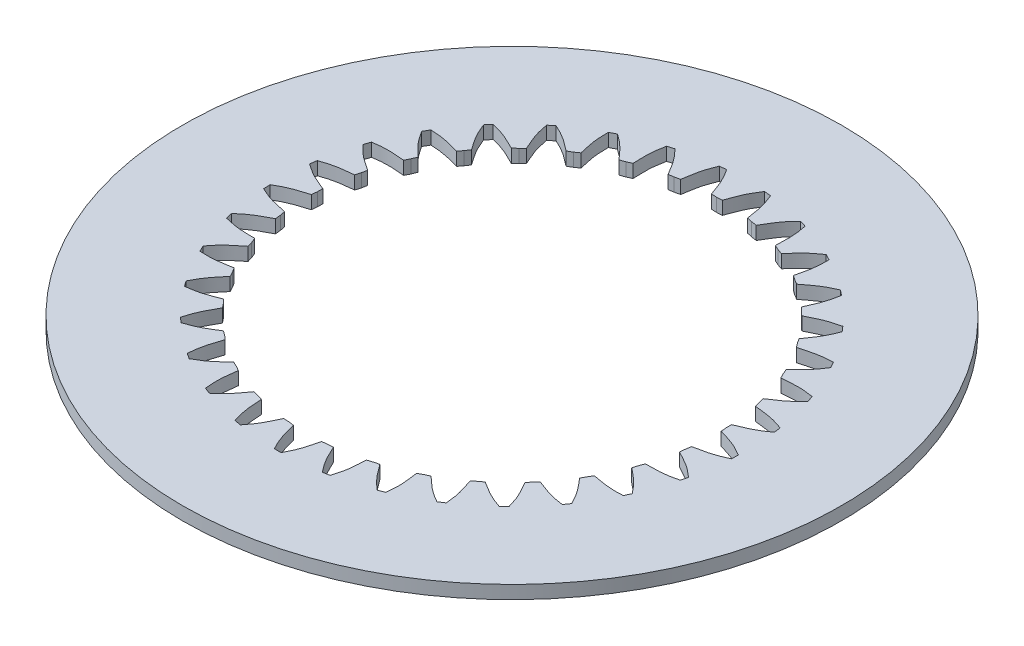
SolidWorks part; units mm, degrees
ref_plane "Plano frontal" through (0, 0, 0) normal (0, 0, 1) x (1, 0, 0)
ref_plane "Plano superior" through (0, 0, 0) normal (0, 1, 0) x (1, 0, 0)
ref_plane "Plano direito" through (0, 0, 0) normal (1, 0, 0) x (0, 0, -1)
sketch "Esboço1" plane through (0, 0, 0) normal (0, 1, 0) x (1, 0, 0)
  line L100 (-38.3877, -48.814) -> (-37.1388, -49.8771)
  line L101 (-39.3009, -59.2517) -> (-37.5711, -60.3634)
  line L102 (-29.9418, -54.5024) -> (-28.4559, -55.1967)
  line L103 (-28.4559, -55.1967) -> (-27.0284, -56.0043)
  line L104 (-27.3773, -65.6187) -> (-25.4682, -66.383)
  line L105 (-19.0861, -59.184) -> (-17.4956, -59.5846)
  line L106 (-17.4956, -59.5846) -> (-15.941, -60.1074)
  line L107 (-14.4641, -69.6141) -> (-12.4449, -70.0032)
  line L108 (-7.5405, -61.7265) -> (-5.903, -61.8189)
  line L109 (-5.903, -61.8189) -> (-4.2776, -62.0381)
  line L110 (-1.0282, -71.0934) -> (1.0282, -71.0934)
  line L111 (4.2776, -62.0381) -> (5.903, -61.8189)
  line L112 (5.903, -61.8189) -> (7.5405, -61.7265)
  line L113 (12.4449, -70.0032) -> (14.4641, -69.6141)
  line L114 (15.941, -60.1074) -> (17.4956, -59.5846)
  line L115 (17.4956, -59.5846) -> (19.0861, -59.184)
  line L116 (25.4682, -66.383) -> (27.3772, -65.6187)
  line L117 (27.0284, -56.0043) -> (28.4559, -55.1967)
  line L118 (28.4559, -55.1967) -> (29.9418, -54.5024)
  line L119 (37.5711, -60.3634) -> (39.3009, -59.2517)
  line L120 (37.1388, -49.8771) -> (38.3877, -48.814)
  line L121 (38.3877, -48.814) -> (39.7154, -47.8509)
  line L122 (48.3159, -52.1622) -> (49.8042, -50.7432)
  line L123 (45.907, -41.9472) -> (46.9321, -40.6669)
  line L124 (46.9321, -40.6669) -> (48.0535, -39.47)
  line L125 (57.3146, -42.0757) -> (58.5074, -40.4007)
  line L126 (53.016, -32.5012) -> (53.7802, -31.05)
  line L127 (53.7802, -31.05) -> (54.6549, -29.6626)
  line L128 (64.2417, -30.4685) -> (65.0959, -28.598)
  line L129 (58.2088, -21.8805) -> (58.6846, -20.3109)
  line L130 (58.6846, -20.3109) -> (59.2808, -18.783)
  line L131 (68.847, -17.7601) -> (69.3318, -15.7617)
  line L132 (61.2978, -10.469) -> (61.468, -8.8378)
  line L133 (61.468, -8.8378) -> (61.7643, -7.2246)
  line L134 (70.9639, -4.4098) -> (71.0618, -2.3558)
  line L135 (62.1713, 1.3208) -> (62.0297, 2.9548)
  line L136 (62.0297, 2.9548) -> (62.0154, 4.5949)
  line L137 (70.5161, 9.1) -> (70.2234, 11.1353)
  line L138 (60.7979, 13.063) -> (60.3496, 14.6406)
  line L139 (60.3496, 14.6406) -> (60.0251, 16.2484)
  line L140 (67.5196, 22.2808) -> (66.847, 24.224)
  line L141 (57.227, 24.333) -> (56.4882, 25.7973)
  line L142 (56.4882, 25.7973) -> (55.8653, 27.3146)
  line L143 (62.0828, 34.6563) -> (61.0546, 36.4371)
  line L144 (51.5878, 34.7235) -> (50.5852, 36.0216)
  line L145 (50.5852, 36.0216) -> (49.6865, 37.3935)
  line L146 (54.4021, 45.7792) -> (53.0555, 47.3333)
  line L147 (44.084, 43.8591) -> (42.854, 44.9439)
  line L148 (42.854, 44.9439) -> (41.7118, 46.121)
  line L149 (44.7552, 55.2476) -> (43.1388, 56.5187)
  line L150 (34.987, 51.4094) -> (33.5738, 52.2419)
  line L151 (33.5738, 52.2419) -> (32.2295, 53.1815)
  line L152 (33.4907, 62.7192) -> (31.663, 63.6615)
  line L153 (24.6254, 57.1017) -> (23.0803, 57.6517)
  line L154 (23.0803, 57.6517) -> (21.5824, 58.32)
  line L155 (21.0158, 67.9239) -> (19.0428, 68.5033)
  line L156 (13.3739, 60.7302) -> (11.7525, 60.9778)
  line L157 (11.7525, 60.9778) -> (10.1553, 61.3506)
  line L158 (7.7814, 70.6737) -> (5.7344, 70.8692)
  line L159 (1.6389, 62.1638) -> (0, 62.1001)
  line L160 (0, 62.1001) -> (-1.6389, 62.1638)
  line L161 (-5.7344, 70.8692) -> (-7.7814, 70.6737)
  line L162 (-10.1553, 61.3506) -> (-11.7525, 60.9778)
  line L163 (-11.7525, 60.9778) -> (-13.3739, 60.7302)
  line L164 (-19.0428, 68.5033) -> (-21.0158, 67.924)
  line L165 (-21.5824, 58.32) -> (-23.0803, 57.6517)
  line L166 (-23.0803, 57.6517) -> (-24.6254, 57.1017)
  line L167 (-31.663, 63.6615) -> (-33.4907, 62.7192)
  line L168 (-32.2295, 53.1815) -> (-33.5738, 52.2419)
  line L169 (-33.5738, 52.2419) -> (-34.987, 51.4094)
  line L170 (-43.1388, 56.5187) -> (-44.7552, 55.2476)
  line L171 (-41.7118, 46.121) -> (-42.854, 44.9439)
  line L172 (-42.854, 44.9439) -> (-44.084, 43.8591)
  line L173 (-53.0555, 47.3333) -> (-54.4021, 45.7792)
  line L174 (-49.6865, 37.3935) -> (-50.5852, 36.0216)
  line L175 (-50.5852, 36.0216) -> (-51.5878, 34.7235)
  line L176 (-61.0546, 36.4371) -> (-62.0828, 34.6563)
  line L177 (-55.8653, 27.3146) -> (-56.4882, 25.7973)
  line L178 (-56.4882, 25.7973) -> (-57.227, 24.333)
  line L179 (-66.847, 24.224) -> (-67.5196, 22.2808)
  line L180 (-60.0251, 16.2484) -> (-60.3496, 14.6407)
  line L181 (-60.3496, 14.6407) -> (-60.7979, 13.063)
  line L182 (-70.2234, 11.1353) -> (-70.5161, 9.1)
  line L183 (-62.0154, 4.5949) -> (-62.0297, 2.9548)
  line L184 (-62.0297, 2.9548) -> (-62.1713, 1.3208)
  line L185 (-71.0618, -2.3558) -> (-70.9639, -4.4097)
  line L186 (-61.7643, -7.2246) -> (-61.468, -8.8378)
  line L187 (-61.468, -8.8378) -> (-61.2978, -10.469)
  line L188 (-69.3318, -15.7617) -> (-68.847, -17.7601)
  line L189 (-59.2808, -18.783) -> (-58.6846, -20.3109)
  line L190 (-58.6846, -20.3109) -> (-58.2088, -21.8805)
  line L191 (-65.0959, -28.598) -> (-64.2417, -30.4685)
  line L192 (-54.6549, -29.6626) -> (-53.7802, -31.05)
  line L193 (-53.7802, -31.05) -> (-53.016, -32.5012)
  line L194 (-58.5074, -40.4007) -> (-57.3146, -42.0757)
  line L195 (-48.0535, -39.47) -> (-46.9321, -40.6669)
  line L196 (-46.9321, -40.6669) -> (-45.907, -41.9472)
  line L197 (-49.8042, -50.7432) -> (-48.316, -52.1622)
  line L198 (-39.7154, -47.8509) -> (-38.3877, -48.814)
  circle A1 centre (0, 0) radius 100
  spline S132 degree 3 poles (-37.1388, -49.8771) (-37.3893, -50.6396) (-37.8968, -52.1594) (-38.8582, -55.2403) (-39.1757, -57.6479) (-39.3009, -59.2517) knots -0.006202 -0.006202 -0.006202 -0.006202 0.243606 0.493415 0.993031 0.993031 0.993031 0.993031
  spline S133 degree 3 poles (-37.5711, -60.3634) (-36.1642, -59.5833) (-34.1061, -58.2943) (-31.703, -56.14) (-30.5314, -55.0469) (-29.9418, -54.5024) knots -0.006202 -0.006202 -0.006202 -0.006202 0.493415 0.743223 0.993031 0.993031 0.993031 0.993031
  spline S134 degree 3 poles (-27.0284, -56.0043) (-27.13, -56.8005) (-27.3407, -58.3889) (-27.7017, -61.596) (-27.5578, -64.0202) (-27.3773, -65.6187) knots -0.006202 -0.006202 -0.006202 -0.006202 0.243606 0.493415 0.993031 0.993031 0.993031 0.993031
  spline S135 degree 3 poles (-25.4682, -66.383) (-24.2345, -65.3507) (-22.4575, -63.6955) (-20.5055, -61.1253) (-19.5619, -59.8302) (-19.0861, -59.184) knots -0.006202 -0.006202 -0.006202 -0.006202 0.493415 0.743223 0.993031 0.993031 0.993031 0.993031
  spline S136 degree 3 poles (-15.941, -60.1074) (-15.8901, -60.9084) (-15.7965, -62.508) (-15.544, -65.7255) (-14.9439, -68.0786) (-14.4641, -69.6141) knots -0.006202 -0.006202 -0.006202 -0.006202 0.243606 0.493415 0.993031 0.993031 0.993031 0.993031
  spline S137 degree 3 poles (-12.4449, -70.0032) (-11.4288, -68.7561) (-9.9972, -66.7946) (-8.5669, -63.9014) (-7.8855, -62.4512) (-7.5405, -61.7265) knots -0.006202 -0.006202 -0.006202 -0.006202 0.493415 0.743223 0.993031 0.993031 0.993031 0.993031
  spline S138 degree 3 poles (-4.2776, -62.0381) (-4.076, -62.8149) (-3.6813, -64.3679) (-2.8244, -67.4795) (-1.7899, -69.6765) (-1.0282, -71.0934) knots -0.006202 -0.006202 -0.006202 -0.006202 0.243606 0.493415 0.993031 0.993031 0.993031 0.993031
  spline S139 degree 3 poles (1.0282, -71.0934) (1.7899, -69.6765) (2.8244, -67.4795) (3.6813, -64.3679) (4.076, -62.8149) (4.2776, -62.0381) knots -0.006202 -0.006202 -0.006202 -0.006202 0.493415 0.743223 0.993031 0.993031 0.993031 0.993031
  spline S140 degree 3 poles (7.5405, -61.7265) (7.8855, -62.4512) (8.5669, -63.9014) (9.9972, -66.7946) (11.4288, -68.7561) (12.4449, -70.0032) knots -0.006202 -0.006202 -0.006202 -0.006202 0.243606 0.493415 0.993031 0.993031 0.993031 0.993031
  spline S141 degree 3 poles (14.4641, -69.6141) (14.9439, -68.0786) (15.544, -65.7255) (15.7965, -62.508) (15.8901, -60.9084) (15.941, -60.1074) knots -0.006202 -0.006202 -0.006202 -0.006202 0.493415 0.743223 0.993031 0.993031 0.993031 0.993031
  spline S142 degree 3 poles (19.0861, -59.184) (19.5619, -59.8302) (20.5055, -61.1253) (22.4575, -63.6955) (24.2345, -65.3507) (25.4682, -66.383) knots -0.006202 -0.006202 -0.006202 -0.006202 0.243606 0.493415 0.993031 0.993031 0.993031 0.993031
  spline S143 degree 3 poles (27.3772, -65.6187) (27.5578, -64.0202) (27.7017, -61.5961) (27.3407, -58.3889) (27.13, -56.8005) (27.0284, -56.0043) knots -0.006202 -0.006202 -0.006202 -0.006202 0.493415 0.743223 0.993031 0.993031 0.993031 0.993031
  spline S144 degree 3 poles (29.9418, -54.5024) (30.5314, -55.0469) (31.703, -56.14) (34.1061, -58.2944) (36.1642, -59.5833) (37.5711, -60.3634) knots -0.006202 -0.006202 -0.006202 -0.006202 0.243606 0.493415 0.993031 0.993031 0.993031 0.993031
  spline S145 degree 3 poles (39.3009, -59.2517) (39.1757, -57.6479) (38.8582, -55.2404) (37.8968, -52.1594) (37.3893, -50.6396) (37.1388, -49.8771) knots -0.006202 -0.006202 -0.006202 -0.006202 0.493415 0.743223 0.993031 0.993031 0.993031 0.993031
  spline S146 degree 3 poles (39.7154, -47.8509) (40.3973, -48.2741) (41.7546, -49.1256) (44.522, -50.7863) (46.7869, -51.6624) (48.3159, -52.1622) knots -0.006202 -0.006202 -0.006202 -0.006202 0.243606 0.493415 0.993031 0.993031 0.993031 0.993031
  spline S147 degree 3 poles (49.8042, -50.7432) (49.3777, -49.1921) (48.6103, -46.8881) (47.0832, -44.0448) (46.2972, -42.6485) (45.907, -41.9472) knots -0.006202 -0.006202 -0.006202 -0.006202 0.493415 0.743223 0.993031 0.993031 0.993031 0.993031
  spline S148 degree 3 poles (48.0535, -39.47) (48.8032, -39.7564) (50.2972, -40.3358) (53.3288, -41.4426) (55.7186, -41.8743) (57.3146, -42.0757) knots -0.006202 -0.006202 -0.006202 -0.006202 0.243606 0.493415 0.993031 0.993031 0.993031 0.993031
  spline S149 degree 3 poles (58.5074, -40.4007) (57.795, -38.9583) (56.6055, -36.8412) (54.5679, -34.3383) (53.5318, -33.116) (53.016, -32.5012) knots -0.006202 -0.006202 -0.006202 -0.006202 0.493415 0.743223 0.993031 0.993031 0.993031 0.993031
  spline S150 degree 3 poles (54.6549, -29.6626) (55.4452, -29.8019) (57.0218, -30.088) (60.2082, -30.6012) (62.6364, -30.5728) (64.2417, -30.4685) knots -0.006202 -0.006202 -0.006202 -0.006202 0.243606 0.493415 0.993031 0.993031 0.993031 0.993031
  spline S151 degree 3 poles (65.0959, -28.598) (64.1235, -27.3165) (62.5548, -25.4628) (60.0804, -23.3907) (58.8317, -22.3866) (58.2088, -21.8805) knots -0.006202 -0.006202 -0.006202 -0.006202 0.493415 0.743223 0.993031 0.993031 0.993031 0.993031
  spline S152 degree 3 poles (59.2808, -18.783) (60.0833, -18.7703) (61.6856, -18.7529) (64.9115, -18.6537) (67.2904, -18.1663) (68.847, -17.7601) knots -0.006202 -0.006202 -0.006202 -0.006202 0.243606 0.493415 0.993031 0.993031 0.993031 0.993031
  spline S153 degree 3 poles (69.3318, -15.7617) (68.1344, -14.6874) (66.2432, -13.1641) (63.4214, -11.5978) (62.0052, -10.8481) (61.2978, -10.469) knots -0.006202 -0.006202 -0.006202 -0.006202 0.493415 0.743223 0.993031 0.993031 0.993031 0.993031
  spline S154 degree 3 poles (61.7643, -7.2246) (62.5498, -7.0602) (64.1198, -6.7399) (67.2687, -6.032) (69.5124, -5.1032) (70.9639, -4.4098) knots -0.006202 -0.006202 -0.006202 -0.006202 0.243606 0.493415 0.993031 0.993031 0.993031 0.993031
  spline S155 degree 3 poles (71.0618, -2.3558) (69.6827, -1.5275) (67.5374, -0.3896) (64.4701, 0.6144) (62.9377, 1.0825) (62.1713, 1.3208) knots -0.006202 -0.006202 -0.006202 -0.006202 0.493415 0.743223 0.993031 0.993031 0.993031 0.993031
  spline S156 degree 3 poles (62.0154, 4.5949) (62.7556, 4.905) (64.2366, 5.5167) (67.1946, 6.8076) (69.222, 8.1443) (70.5161, 9.1) knots -0.006202 -0.006202 -0.006202 -0.006202 0.243606 0.493415 0.993031 0.993031 0.993031 0.993031
  spline S157 degree 3 poles (70.2234, 11.1353) (68.7126, 11.6877) (66.3907, 12.399) (63.1888, 12.8043) (61.5955, 12.974) (60.7979, 13.063) knots -0.006202 -0.006202 -0.006202 -0.006202 0.493415 0.743223 0.993031 0.993031 0.993031 0.993031
  spline S158 degree 3 poles (60.0251, 16.2484) (60.6933, 16.6929) (62.0318, 17.5738) (64.6919, 19.4013) (66.4298, 21.0975) (67.5196, 22.2808) knots -0.006202 -0.006202 -0.006202 -0.006202 0.243606 0.493415 0.993031 0.993031 0.993031 0.993031
  spline S159 degree 3 poles (66.847, 24.224) (65.2589, 24.4804) (62.8444, 24.7395) (59.6237, 24.5315) (58.027, 24.3966) (57.227, 24.333) knots -0.006202 -0.006202 -0.006202 -0.006202 0.493415 0.743223 0.993031 0.993031 0.993031 0.993031
  spline S160 degree 3 poles (55.8653, 27.3146) (56.4373, 27.8775) (57.5849, 28.9958) (59.8512, 31.2937) (61.2366, 33.2882) (62.0828, 34.6563) knots -0.006202 -0.006202 -0.006202 -0.006202 0.243606 0.493415 0.993031 0.993031 0.993031 0.993031
  spline S161 degree 3 poles (61.0546, 36.4371) (59.4467, 36.3883) (57.0267, 36.1858) (53.9036, 35.3721) (52.3613, 34.9374) (51.5878, 34.7235) knots -0.006202 -0.006202 -0.006202 -0.006202 0.493415 0.743223 0.993031 0.993031 0.993031 0.993031
  spline S162 degree 3 poles (49.6865, 37.3935) (50.1416, 38.0546) (51.0568, 39.3699) (52.8472, 42.0551) (53.8301, 44.2757) (54.4021, 45.7792) knots -0.006202 -0.006202 -0.006202 -0.006202 0.243606 0.493415 0.993031 0.993031 0.993031 0.993031
  spline S163 degree 3 poles (53.0555, 47.3333) (51.4859, 46.9811) (49.148, 46.3242) (46.2353, 44.9342) (44.8031, 44.2155) (44.084, 43.8591) knots -0.006202 -0.006202 -0.006202 -0.006202 0.493415 0.743223 0.993031 0.993031 0.993031 0.993031
  spline S164 degree 3 poles (41.7118, 46.121) (42.0336, 46.8562) (42.6833, 48.3209) (43.9332, 51.2965) (44.4781, 53.663) (44.7552, 55.2476) knots -0.006202 -0.006202 -0.006202 -0.006202 0.243606 0.493415 0.993031 0.993031 0.993031 0.993031
  spline S165 degree 3 poles (43.1388, 56.5187) (41.6642, 55.8759) (39.4929, 54.7884) (36.8959, 52.8722) (35.6257, 51.8955) (34.987, 51.4094) knots -0.006202 -0.006202 -0.006202 -0.006202 0.493415 0.743223 0.993031 0.993031 0.993031 0.993031
  spline S166 degree 3 poles (32.2295, 53.1815) (32.4064, 53.9644) (32.7672, 55.5256) (33.4313, 58.6839) (33.5185, 61.1108) (33.4907, 62.7192) knots -0.006202 -0.006202 -0.006202 -0.006202 0.243606 0.493415 0.993031 0.993031 0.993031 0.993031
  spline S167 degree 3 poles (31.663, 63.6615) (30.3367, 62.7511) (28.4104, 61.2724) (26.223, 58.8993) (25.1606, 57.6999) (24.6254, 57.1017) knots -0.006202 -0.006202 -0.006202 -0.006202 0.493415 0.743223 0.993031 0.993031 0.993031 0.993031
  spline S168 degree 3 poles (21.5824, 58.32) (21.6079, 59.1221) (21.6667, 60.7234) (21.7212, 63.9504) (21.3475, 66.3498) (21.0158, 67.9239) knots -0.006202 -0.006202 -0.006202 -0.006202 0.243606 0.493415 0.993031 0.993031 0.993031 0.993031
  spline S169 degree 3 poles (19.0428, 68.5033) (17.9127, 67.3584) (16.3012, 65.5418) (14.6023, 62.7977) (13.7861, 61.4188) (13.3739, 60.7302) knots -0.006202 -0.006202 -0.006202 -0.006202 0.493415 0.743223 0.993031 0.993031 0.993031 0.993031
  spline S170 degree 3 poles (10.1553, 61.3506) (10.0285, 62.143) (9.7832, 63.7265) (9.226, 66.9054) (8.405, 69.1909) (7.7814, 70.6737) knots -0.006202 -0.006202 -0.006202 -0.006202 0.243606 0.493415 0.993031 0.993031 0.993031 0.993031
  spline S171 degree 3 poles (5.7344, 70.8692) (4.8414, 69.5311) (3.6027, 67.4424) (2.4539, 64.4264) (1.9134, 62.9179) (1.6389, 62.1638) knots -0.006202 -0.006202 -0.006202 -0.006202 0.493415 0.743223 0.993031 0.993031 0.993031 0.993031
  spline S172 degree 3 poles (-1.6389, 62.1638) (-1.9134, 62.9179) (-2.4539, 64.4264) (-3.6027, 67.4424) (-4.8414, 69.5311) (-5.7344, 70.8692) knots -0.006202 -0.006202 -0.006202 -0.006202 0.243606 0.493415 0.993031 0.993031 0.993031 0.993031
  spline S173 degree 3 poles (-7.7814, 70.6737) (-8.405, 69.1909) (-9.226, 66.9054) (-9.7832, 63.7265) (-10.0285, 62.143) (-10.1553, 61.3506) knots -0.006202 -0.006202 -0.006202 -0.006202 0.493415 0.743223 0.993031 0.993031 0.993031 0.993031
  spline S174 degree 3 poles (-13.3739, 60.7302) (-13.7861, 61.4188) (-14.6023, 62.7977) (-16.3011, 65.5418) (-17.9127, 67.3584) (-19.0428, 68.5033) knots -0.006202 -0.006202 -0.006202 -0.006202 0.243606 0.493415 0.993031 0.993031 0.993031 0.993031
  spline S175 degree 3 poles (-21.0158, 67.924) (-21.3475, 66.3498) (-21.7212, 63.9504) (-21.6667, 60.7234) (-21.6079, 59.1221) (-21.5824, 58.32) knots -0.006202 -0.006202 -0.006202 -0.006202 0.493415 0.743223 0.993031 0.993031 0.993031 0.993031
  spline S176 degree 3 poles (-24.6254, 57.1017) (-25.1606, 57.6999) (-26.223, 58.8993) (-28.4104, 61.2724) (-30.3367, 62.7511) (-31.663, 63.6615) knots -0.006202 -0.006202 -0.006202 -0.006202 0.243606 0.493415 0.993031 0.993031 0.993031 0.993031
  spline S177 degree 3 poles (-33.4907, 62.7192) (-33.5185, 61.1108) (-33.4313, 58.6839) (-32.7672, 55.5256) (-32.4064, 53.9644) (-32.2295, 53.1815) knots -0.006202 -0.006202 -0.006202 -0.006202 0.493415 0.743223 0.993031 0.993031 0.993031 0.993031
  spline S178 degree 3 poles (-34.987, 51.4094) (-35.6256, 51.8955) (-36.8959, 52.8722) (-39.4929, 54.7884) (-41.6642, 55.8759) (-43.1388, 56.5187) knots -0.006202 -0.006202 -0.006202 -0.006202 0.243606 0.493415 0.993031 0.993031 0.993031 0.993031
  spline S179 degree 3 poles (-44.7552, 55.2476) (-44.4781, 53.663) (-43.9332, 51.2965) (-42.6833, 48.3209) (-42.0336, 46.8562) (-41.7118, 46.121) knots -0.006202 -0.006202 -0.006202 -0.006202 0.493415 0.743223 0.993031 0.993031 0.993031 0.993031
  spline S180 degree 3 poles (-44.084, 43.8591) (-44.8031, 44.2155) (-46.2353, 44.9342) (-49.148, 46.3242) (-51.4859, 46.9811) (-53.0555, 47.3333) knots -0.006202 -0.006202 -0.006202 -0.006202 0.243606 0.493415 0.993031 0.993031 0.993031 0.993031
  spline S181 degree 3 poles (-54.4021, 45.7792) (-53.8301, 44.2757) (-52.8472, 42.0551) (-51.0568, 39.3699) (-50.1416, 38.0546) (-49.6865, 37.3935) knots -0.006202 -0.006202 -0.006202 -0.006202 0.493415 0.743223 0.993031 0.993031 0.993031 0.993031
  spline S182 degree 3 poles (-51.5878, 34.7235) (-52.3613, 34.9374) (-53.9036, 35.3721) (-57.0267, 36.1858) (-59.4467, 36.3883) (-61.0546, 36.4371) knots -0.006202 -0.006202 -0.006202 -0.006202 0.243606 0.493415 0.993031 0.993031 0.993031 0.993031
  spline S183 degree 3 poles (-62.0828, 34.6563) (-61.2366, 33.2882) (-59.8512, 31.2937) (-57.5849, 28.9958) (-56.4373, 27.8775) (-55.8653, 27.3146) knots -0.006202 -0.006202 -0.006202 -0.006202 0.493415 0.743223 0.993031 0.993031 0.993031 0.993031
  spline S184 degree 3 poles (-57.227, 24.333) (-58.027, 24.3966) (-59.6237, 24.5315) (-62.8444, 24.7395) (-65.2589, 24.4804) (-66.847, 24.224) knots -0.006202 -0.006202 -0.006202 -0.006202 0.243606 0.493415 0.993031 0.993031 0.993031 0.993031
  spline S185 degree 3 poles (-67.5196, 22.2808) (-66.4298, 21.0975) (-64.6919, 19.4013) (-62.0318, 17.5738) (-60.6933, 16.6929) (-60.0251, 16.2484) knots -0.006202 -0.006202 -0.006202 -0.006202 0.493415 0.743223 0.993031 0.993031 0.993031 0.993031
  spline S186 degree 3 poles (-60.7979, 13.063) (-61.5955, 12.974) (-63.1888, 12.8044) (-66.3907, 12.399) (-68.7126, 11.6877) (-70.2234, 11.1353) knots -0.006202 -0.006202 -0.006202 -0.006202 0.243606 0.493415 0.993031 0.993031 0.993031 0.993031
  spline S187 degree 3 poles (-70.5161, 9.1) (-69.222, 8.1443) (-67.1946, 6.8077) (-64.2366, 5.5167) (-62.7556, 4.905) (-62.0154, 4.5949) knots -0.006202 -0.006202 -0.006202 -0.006202 0.493415 0.743223 0.993031 0.993031 0.993031 0.993031
  spline S188 degree 3 poles (-62.1713, 1.3208) (-62.9377, 1.0825) (-64.4701, 0.6144) (-67.5374, -0.3896) (-69.6827, -1.5275) (-71.0618, -2.3558) knots -0.006202 -0.006202 -0.006202 -0.006202 0.243606 0.493415 0.993031 0.993031 0.993031 0.993031
  spline S189 degree 3 poles (-70.9639, -4.4097) (-69.5124, -5.1032) (-67.2687, -6.032) (-64.1198, -6.7399) (-62.5498, -7.0602) (-61.7643, -7.2246) knots -0.006202 -0.006202 -0.006202 -0.006202 0.493415 0.743223 0.993031 0.993031 0.993031 0.993031
  spline S190 degree 3 poles (-61.2978, -10.469) (-62.0052, -10.8481) (-63.4214, -11.5978) (-66.2432, -13.1641) (-68.1344, -14.6874) (-69.3318, -15.7617) knots -0.006202 -0.006202 -0.006202 -0.006202 0.243606 0.493415 0.993031 0.993031 0.993031 0.993031
  spline S191 degree 3 poles (-68.847, -17.7601) (-67.2904, -18.1663) (-64.9115, -18.6537) (-61.6856, -18.7528) (-60.0833, -18.7703) (-59.2808, -18.783) knots -0.006202 -0.006202 -0.006202 -0.006202 0.493415 0.743223 0.993031 0.993031 0.993031 0.993031
  spline S192 degree 3 poles (-58.2088, -21.8805) (-58.8317, -22.3866) (-60.0804, -23.3907) (-62.5548, -25.4628) (-64.1235, -27.3165) (-65.0959, -28.598) knots -0.006202 -0.006202 -0.006202 -0.006202 0.243606 0.493415 0.993031 0.993031 0.993031 0.993031
  spline S193 degree 3 poles (-64.2417, -30.4685) (-62.6364, -30.5728) (-60.2082, -30.6012) (-57.0218, -30.088) (-55.4452, -29.8019) (-54.6549, -29.6626) knots -0.006202 -0.006202 -0.006202 -0.006202 0.493415 0.743223 0.993031 0.993031 0.993031 0.993031
  spline S194 degree 3 poles (-53.016, -32.5012) (-53.5318, -33.116) (-54.5679, -34.3383) (-56.6055, -36.8412) (-57.795, -38.9583) (-58.5074, -40.4007) knots -0.006202 -0.006202 -0.006202 -0.006202 0.243606 0.493415 0.993031 0.993031 0.993031 0.993031
  spline S195 degree 3 poles (-57.3146, -42.0757) (-55.7186, -41.8743) (-53.3288, -41.4426) (-50.2972, -40.3357) (-48.8032, -39.7564) (-48.0535, -39.47) knots -0.006202 -0.006202 -0.006202 -0.006202 0.493415 0.743223 0.993031 0.993031 0.993031 0.993031
  spline S196 degree 3 poles (-45.907, -41.9472) (-46.2972, -42.6485) (-47.0832, -44.0448) (-48.6103, -46.8881) (-49.3777, -49.1921) (-49.8042, -50.7432) knots -0.006202 -0.006202 -0.006202 -0.006202 0.243606 0.493415 0.993031 0.993031 0.993031 0.993031
  spline S197 degree 3 poles (-48.316, -52.1622) (-46.7869, -51.6624) (-44.522, -50.7863) (-41.7546, -49.1256) (-40.3973, -48.2741) (-39.7154, -47.8509) knots -0.006202 -0.006202 -0.006202 -0.006202 0.493415 0.743223 0.993031 0.993031 0.993031 0.993031
  point P303 (0, 0)
  dimension "D1" = 33
extrude "Ressalto-extrusão2" add sketch "Esboço1" along normal blind 4
